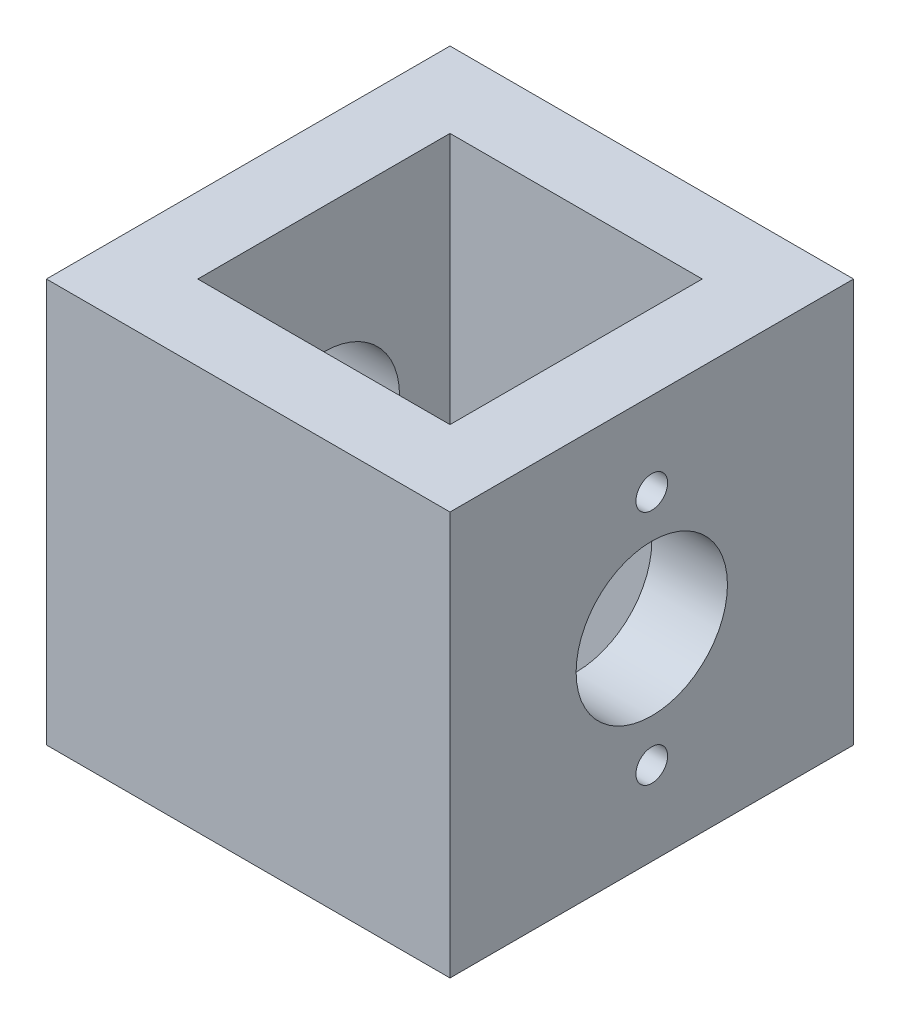
SolidWorks part; units mm, degrees
material "6061 Alloy"
ref_plane "Front Plane" through (0, 0, 0) normal (0, 0, 1) x (1, 0, 0)
ref_plane "Top Plane" through (0, 0, 0) normal (0, 1, 0) x (1, 0, 0)
ref_plane "Right Plane" through (0, 0, 0) normal (1, 0, 0) x (0, 0, -1)
sketch "Sketch1" plane through (0, 0, 0) normal (0, 1, 0) x (1, 0, 0)
  line L1 (0, 0) -> (25.4, 0)
  line L2 (0, 0) -> (0, 25.4)
  line L3 (0, 25.4) -> (25.4, 25.4)
  line L4 (25.4, 0) -> (25.4, 25.4)
  dimension "D1" = 25.4
  dimension "D2" = 25.4
extrude "Boss-Extrude1" add sketch "Sketch1" along normal blind 25.4
sketch "Sketch2" plane through (0, 25.4, 0) normal (0, 1, 0) x (1, 0, 0)
  line L0 (25.4, 0) -> (25.4, 25.4) construction
  line L1 (4.7625, 4.7625) -> (20.6375, 4.7625)
  line L2 (4.7625, 4.7625) -> (4.7625, 20.6375)
  line L3 (4.7625, 20.6375) -> (20.6375, 20.6375)
  line L4 (20.6375, 4.7625) -> (20.6375, 20.6375)
  line L5 (4.7625, 4.7625) -> (20.6375, 20.6375) construction
  line L6 (4.7625, 20.6375) -> (20.6375, 4.7625) construction
  line L7 (25.4, 25.4) -> (0, 25.4) construction
  point P0 (12.7, 12.7)
  point P7 (25.4, 12.7)
  point P10 (12.7, 25.4)
  dimension "D1" = 15.875
  dimension "D2" = 15.875
extrude "Cut-Extrude1" cut sketch "Sketch2" against normal through all
hole_wizard "Tap Drill for #4-40 Tap1" positions "Sketch4" profile "Sketch3" hole size "#4-40" standard "ANSI Inch"
sketch "Sketch4" plane through (0, 0, 0) normal (0, -1, 0) x (-1, 0, 0)
  line L0 (0, 25.4) -> (0, 0) construction
  line L1 (-25.4, 25.4) -> (0, 25.4) construction
  line L2 (-25.4, 0) -> (-25.4, 25.4) construction
  line L3 (0, 0) -> (-25.4, 0) construction
  point P0 (-2.54, 2.54)
  point P2 (-22.86, 2.54)
  point P4 (-22.86, 22.86)
  point P6 (-2.54, 22.86)
  dimension "D1" = 2.54
  dimension "D2" = 2.54
  dimension "D3" = 2.54
  dimension "D4" = 2.54
sketch "Sketch3" plane through (2.54, 0, -2.54) normal (1, 0, 0) x (0, 0, -1)
  line L0 (0, 0) -> (0, 11.398)
  line L1 (0, 11.398) -> (1.1303, 10.7188)
  line L2 (1.1303, 10.7188) -> (1.1303, 0)
  line L5 (1.1303, 0) -> (0, 0)
  line L10 (0, 11.398) -> (-1.1303, 10.7188) construction
  line L11 (0, -6.35) -> (0, 107.95) construction
  dimension "Hole Dia." = 2.2606
  dimension "Hole Depth" = 10.7188
  dimension "Drill Angle" = 118
hole_wizard "3/8 (0.375) Diameter Hole1" positions "Sketch6" profile "Sketch5" hole size "3/8" standard "ANSI Inch" end condition through all
sketch "Sketch6" plane through (25.4, 0, 0) normal (1, 0, 0) x (0, 0, -1)
  line L0 (0, 25.4) -> (25.4, 25.4) construction
  line L1 (25.4, 25.4) -> (25.4, 0) construction
  point P1 (12.7, 12.7)
  point P6 (12.7, 25.4)
  point P9 (25.4, 12.7)
sketch "Sketch5" plane through (25.4, 12.7, -12.7) normal (0, 1, 0) x (0, 0, -1)
  line L0 (0, 0) -> (0, 25.4)
  line L1 (0, 25.4) -> (4.7625, 25.4)
  line L2 (4.7625, 25.4) -> (4.7625, 0)
  line L5 (4.7625, 0) -> (0, 0)
  line L11 (0, -6.35) -> (0, 107.95) construction
  dimension "Thru Hole Dia." = 9.525
  dimension "Thru Hole Depth" = 25.4
hole_wizard "Tap Drill for #3-48 Tap1" positions "Sketch8" profile "Sketch7" hole size "#3-48" standard "ANSI Inch" end condition up to next
sketch "Sketch8" plane through (25.4, 0, 0) normal (1, 0, 0) x (0, 0, -1)
  line L0 (0, 25.4) -> (25.4, 25.4) construction
  point P0 (12.7, 20.1422)
  point P2 (12.7, 5.2578)
  point P7 (12.7, 25.4)
  dimension "D1" = 14.8844
  dimension "D2" = 5.2578
sketch "Sketch7" plane through (25.4, 20.1422, -12.7) normal (0, 1, 0) x (0, 0, -1)
  line L0 (0, 0) -> (0, 4.7625)
  line L1 (0, 4.7625) -> (0.9969, 4.7625)
  line L2 (0.9969, 4.7625) -> (0.9969, 0)
  line L5 (0.9969, 0) -> (0, 0)
  line L11 (0, -6.35) -> (0, 107.95) construction
  dimension "Thru Hole Dia." = 1.9939
  dimension "Thru Hole Depth" = 4.7625
